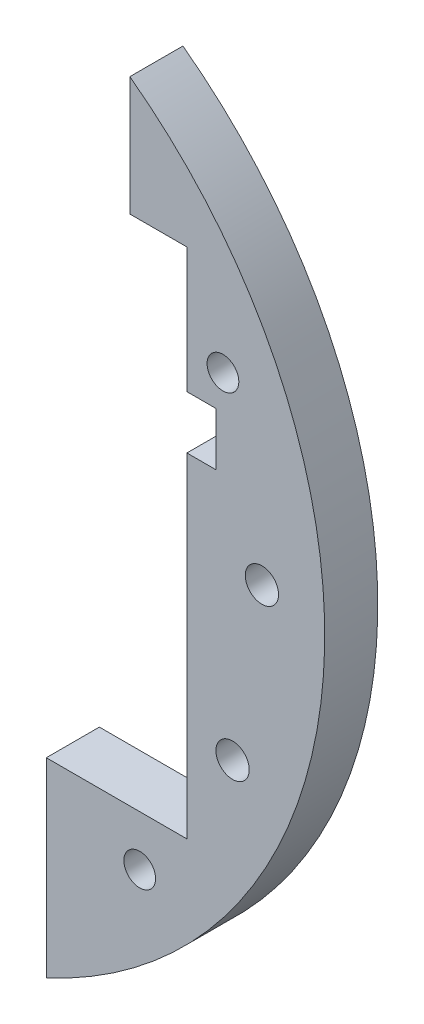
SolidWorks part; units mm, degrees
material "Balsa"
ref_plane "Front Plane" through (0, 0, 0) normal (0, 0, 1) x (1, 0, 0)
ref_plane "Top Plane" through (0, 0, 0) normal (0, 1, 0) x (1, 0, 0)
ref_plane "Right Plane" through (0, 0, 0) normal (1, 0, 0) x (0, 0, -1)
sketch "Sketch1" plane through (0, 0, 0) normal (0, 0, 1) x (1, 0, 0)
  line L0 (45.3154, 21.1309) -> (0, 0) construction
  line L1 (0, 0) -> (35.3553, -35.3553) construction
  line L2 (49.9788, 1.4542) -> (0, 0) construction
  line L3 (0, 0) -> (46.4674, -18.4603) construction
  circle A0 centre (45.3154, 21.1309) radius 1.8986
  circle A1 centre (49.9788, 1.4542) radius 1.9939
  circle A2 centre (0, 0) radius 57.5
  circle A3 centre (0, 0) radius 8
  circle A4 centre (0, 0) radius 16.5 construction
  circle A5 centre (46.4674, -18.4603) radius 1.9939
  circle A6 centre (0, 0) radius 50 construction
  circle A27 centre (0, -16.5) radius 1.9939
  circle A28 centre (11.6673, -11.6673) radius 1.8986 construction
  circle A30 centre (0, -50) radius 1.8986
  circle A31 centre (-16.5, 0) radius 1.9939
  circle A32 centre (-11.6673, -11.6673) radius 1.8986
  circle A33 centre (0, 16.5) radius 1.9939
  circle A34 centre (-11.6673, 11.6673) radius 1.8986
  circle A35 centre (16.5, 0) radius 1.9939 construction
  circle A36 centre (11.6673, 11.6673) radius 1.8986
  circle A38 centre (-35.3553, -35.3553) radius 1.8986
  circle A40 centre (-50, 0) radius 1.8986
  circle A42 centre (-35.3553, 35.3553) radius 1.8986
  circle A44 centre (0, 50) radius 1.8986
  circle A46 centre (35.3553, 35.3553) radius 1.8986 construction
  circle A48 centre (50, 0) radius 1.8986 construction
  circle A50 centre (35.3553, -35.3553) radius 1.8986
  dimension "D1" = 115
  dimension "D4" = 70
  dimension "D6" = 100
  dimension "D7" = 23.333
  dimension "D8" = 33
  dimension "D9" = 3.7973
  dimension "D10" = 3.9878
  dimension "D15" = 3.7973
  dimension "D17" = 3.9878
  dimension "D18" = 3.7973
  dimension "D3" = 16
  dimension "D11" = 3.9878
  dimension "D5" = 23.333
  dimension "D19" = 45
  dimension "D20" = 4
  dimension "D21" = 8
extrude "Boss-Extrude1" add sketch "Sketch1" along normal blind 6.35
sketch "Sketch2" plane through (0, 0, 0) normal (0, 0, 1) x (1, 0, 0)
  line L0 (12.5, -29.35) -> (41, -29.35)
  line L1 (41, -29.35) -> (41, 10.65)
  line L2 (41, 10.65) -> (44.5, 10.65)
  line L3 (44.5, 10.65) -> (44.5, 17)
  line L4 (44.5, 17) -> (41, 17)
  line L5 (41, 17) -> (41, 32)
  line L6 (41, 32) -> (21, 32)
  line L7 (21, 32) -> (21, 17)
  line L8 (21, 17) -> (17.5, 17)
  line L9 (17.5, 17) -> (17.5, 10.65)
  line L10 (17.5, 10.65) -> (21, 10.65)
  line L11 (21, 10.65) -> (21, 5.65)
  line L12 (21, 5.65) -> (12.5, 5.65)
  line L13 (12.5, 5.65) -> (12.5, -29.35)
  dimension "D1" = 20
  dimension "D2" = 3.5
  dimension "D3" = 3.5
  dimension "D4" = 15
  dimension "D5" = 6.35
  dimension "D6" = 5
  dimension "D7" = 40
  dimension "D8" = 8.5
  dimension "D9" = 32
  dimension "D10" = 21
extrude "Cut-Extrude1" cut sketch "Sketch2" along normal through all
sketch "Sketch3" plane through (0, 0, 0) normal (0, 0, -1) x (-1, 0, 0)
  line L0 (-41, 32) -> (-21, 32) construction
  line L1 (-34.175, -8) -> (-27.825, -8)
  line L2 (-34.175, -8) -> (-34.175, 72)
  line L3 (-34.175, 72) -> (-27.825, 72)
  line L4 (-27.825, -8) -> (-27.825, 72)
  line L5 (-34.175, -8) -> (-27.825, 72) construction
  line L6 (-34.175, 72) -> (-27.825, -8) construction
  point P0 (-31, 32)
  dimension "D1" = 6.35
  dimension "D2" = 80
extrude "Cut-Extrude3" cut sketch "Sketch3" against normal through all
sketch "Sketch4" plane through (0, 0, 0) normal (0, 0, 1) x (1, 0, 0)
  line L0 (21, -36.5) -> (21, -5.3721)
  line L1 (21, -5.3721) -> (24.175, -5.4115)
  line L2 (24.175, -5.4115) -> (24.175, -57.5)
  line L3 (0, -57.5) -> (24.175, -57.5)
  line L4 (0, 0) -> (82.9328, 0) construction
  line L5 (34.175, 32) -> (27.825, 32) construction
  line L6 (0, 57.5) -> (24.175, 57.5)
  line L7 (24.175, 5.4115) -> (24.175, 57.5)
  line L8 (21, 5.3721) -> (24.175, 5.4115)
  line L9 (21, 36.5) -> (21, 5.3721)
  arc A0 (0, -57.5) -> (21, -36.5) centre (0, -36.5) ccw
  arc A1 (0, 57.5) -> (21, 36.5) centre (0, 36.5) cw
  arc A2 (27.825, 50.3192) -> (34.175, 46.242) centre (0, 0) ccw construction
  point P13 (31, 32)
  point P16 (22.5875, -5.3918)
  dimension "D2" = 3.175
  dimension "D4" = 8.4125
extrude "Cut-Extrude5" cut sketch "Sketch4" along normal through all
sketch "Sketch5" plane through (0, 0, 6.35) normal (0, 0, 1) x (1, 0, 0)
  line L3 (24.175, 52.1711) -> (24.175, 32)
  line L4 (24.175, 32) -> (27.825, 32)
  line L5 (27.825, 32) -> (27.825, 50.3192)
  line L6 (24.175, 52.1711) -> (24.175, 32)
  line L7 (24.175, 32) -> (27.825, 32)
  line L8 (27.825, 32) -> (27.825, 50.3192)
  arc A1 (27.825, 50.3192) -> (24.175, 52.1711) centre (0, 0) ccw
  arc A2 (27.825, 50.3192) -> (24.175, 52.1711) centre (0, 0) ccw
  dimension "D1" = 0
extrude "Cut-Extrude6" cut sketch "Sketch5" against normal through all
